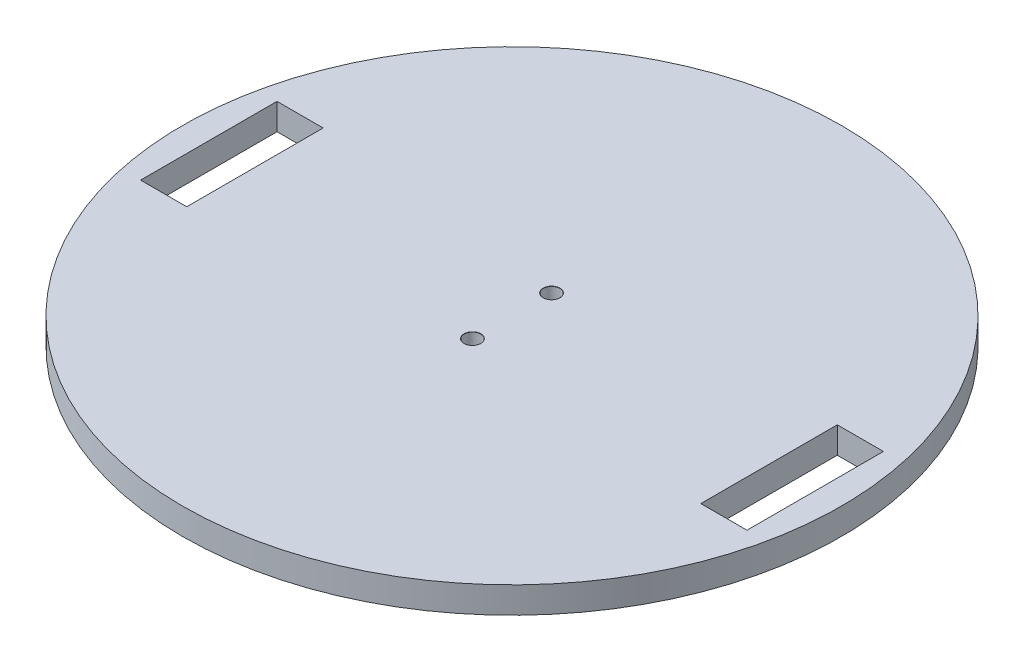
SolidWorks part; units mm, degrees
ref_plane "Front Plane" through (0, 0, 0) normal (0, 0, 1) x (1, 0, 0)
ref_plane "Top Plane" through (0, 0, 0) normal (0, 1, 0) x (1, 0, 0)
ref_plane "Right Plane" through (0, 0, 0) normal (1, 0, 0) x (0, 0, -1)
sketch "Sketch2" plane through (0, 0, 0) normal (0, 1, 0) x (1, 0, 0)
  circle A0 centre (0, 0) radius 50
  dimension "D1" = 100
extrude "Boss-Extrude2" add sketch "Sketch2" along normal blind 4
hole_wizard "Tap Drill for M3x0.5 Tap1" positions "Sketch3" profile "Sketch4" hole size "M3x0.5" standard "ANSI Metric" end condition through all
sketch "Sketch3" plane through (0, 4, 0) normal (0, 1, 0) x (1, 0, 0)
  point P0 (0, 6)
  point P2 (0, -6)
  dimension "D1" = 6
  dimension "D2" = 6
sketch "Sketch4" plane through (0, 4, -6) normal (1, 0, 0) x (0, 0, 1)
  line L0 (0, 0) -> (0, 4)
  line L1 (0, 4) -> (1.25, 4)
  line L2 (1.25, 4) -> (1.25, 0.025)
  line L3 (1.25, 0.025) -> (1.275, 0)
  line L5 (1.275, 0) -> (0, 0)
  line L6 (-1.25, 0.025) -> (-1.275, 0) construction
  line L11 (0, -6.35) -> (0, 107.95) construction
  dimension "Thru Hole Dia." = 2.5
  dimension "Thru Hole Depth" = 4
  dimension "Near C'Sink Dia." = 2.55
  dimension "Near C'Sink Angle" = 90
sketch "Sketch5" plane through (0, 0, 0) normal (0, -1, 0) x (1, 0, 0)
  line L3 (-39, -10.35) -> (-46, -10.35)
  line L4 (-39, -10.35) -> (-39, 10.35)
  line L5 (-39, 10.35) -> (-46, 10.35)
  line L6 (-46, -10.35) -> (-46, 10.35)
  line L9 (39, -10.35) -> (46, -10.35)
  line L10 (39, -10.35) -> (39, 10.35)
  line L11 (39, 10.35) -> (46, 10.35)
  line L12 (46, -10.35) -> (46, 10.35)
  point P0 (-39, 0)
  point P3 (39, 0)
  dimension "D1" = 20.7
  dimension "D2" = 7
  dimension "D3" = 20.7
  dimension "D4" = 7
  dimension "D5" = 39
  dimension "D6" = 39
extrude "Cut-Extrude1" cut sketch "Sketch5" against normal blind 10 contours L6 L3 L4 L5 | L9 L12 L11 L10
